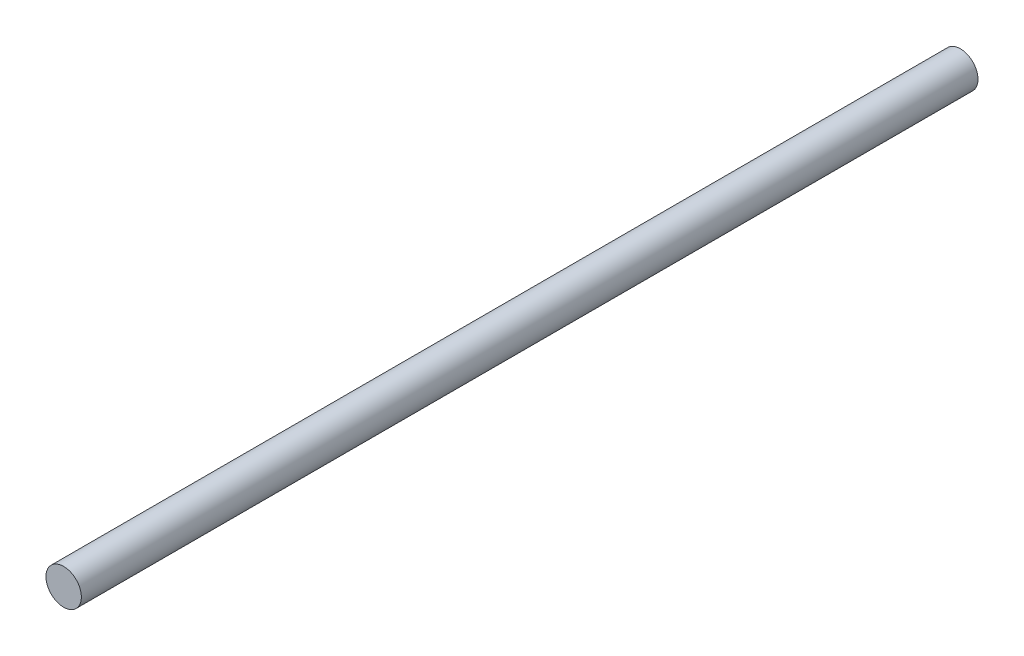
SolidWorks part; units mm, degrees
ref_plane "Front Plane" through (0, 0, 0) normal (0, 0, 1) x (1, 0, 0)
ref_plane "Top Plane" through (0, 0, 0) normal (0, 1, 0) x (1, 0, 0)
ref_plane "Right Plane" through (0, 0, 0) normal (1, 0, 0) x (0, 0, -1)
sketch "Sketch1" plane through (0, 0, 0) normal (0, 0, 1) x (1, 0, 0)
  circle A0 centre (0, 0) radius 4.7625
extrude "Boss-Extrude1" add sketch "Sketch1" along normal blind 241.3
